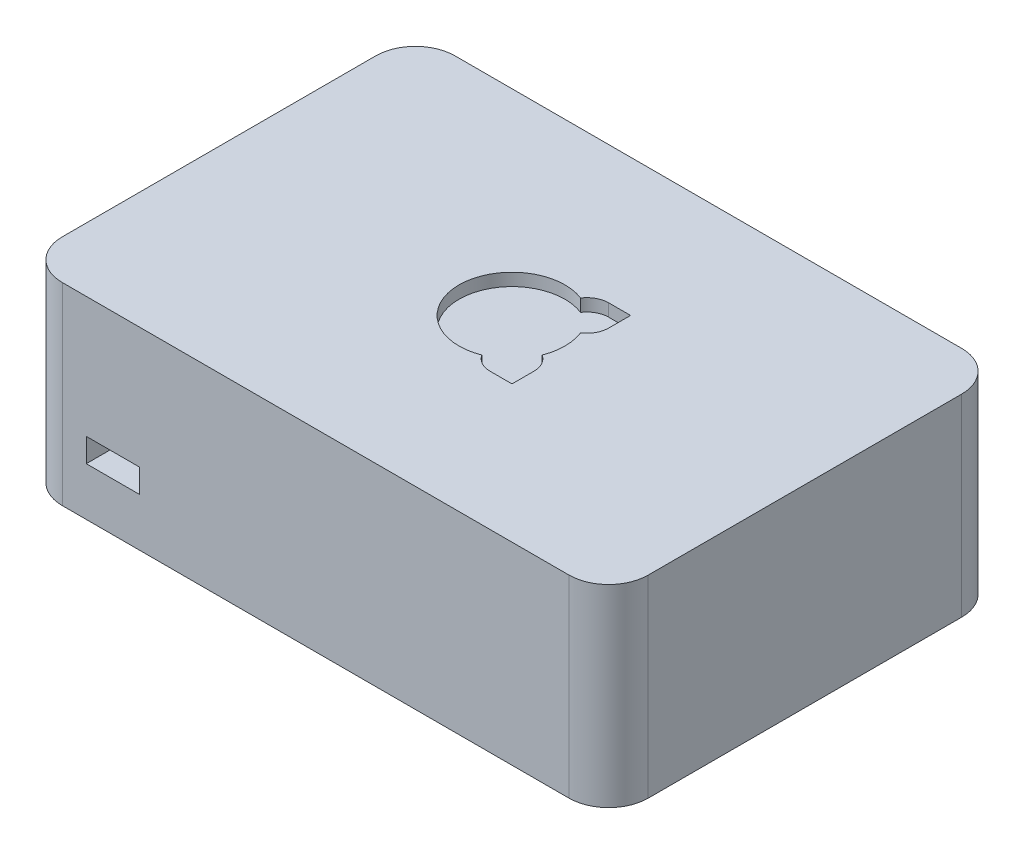
SolidWorks part; units mm, degrees
ref_plane "Front Plane" through (0, 0, 0) normal (0, 0, 1) x (1, 0, 0)
ref_plane "Top Plane" through (0, 0, 0) normal (0, 1, 0) x (1, 0, 0)
ref_plane "Right Plane" through (0, 0, 0) normal (1, 0, 0) x (0, 0, -1)
sketch "Sketch1" plane through (0, 0, 0) normal (0, 1, 0) x (1, 0, 0)
  line L1 (0, 0) -> (94, 0)
  line L2 (0, 0) -> (0, 63)
  line L3 (0, 63) -> (94, 63)
  line L4 (94, 0) -> (94, 63)
  dimension "D1" = 63
  dimension "D2" = 94
extrude "Boss-Extrude1" add sketch "Sketch1" along normal blind 31 contours L2 L3 L4 L1
fillet "Fillet1" radius 6.35 4 edges at (0, 15.5, -63) (94, 15.5, -63) (94, 15.5, 0) (0, 15.5, 0)
sketch "Sketch3" plane through (0, 0, -63) normal (0, 0, -1) x (-1, 0, 0)
  line L0 (-6.35, 31) -> (-87.65, 31) construction
  line L1 (-12, 26.46) -> (-62.5, 26.46)
  line L2 (-12, 26.46) -> (-12, 28.46)
  line L3 (-12, 28.46) -> (-62.5, 28.46)
  line L4 (-62.5, 26.46) -> (-62.5, 28.46)
  line L5 (0, 31) -> (0, 0) construction
  dimension "D1" = 50.5
  dimension "D2" = 2
  dimension "D3" = 2.54
  dimension "D4" = 12
extrude "Boss-Extrude2" add sketch "Sketch3" along normal blind 2.5
sketch "Sketch4" plane through (0, 0, 0) normal (0, 0, 1) x (1, 0, 0)
  line L0 (6.35, 0) -> (87.65, 0) construction
  line L1 (10.2, 7.75) -> (18.7, 7.75)
  line L2 (10.2, 7.75) -> (10.2, 11.55)
  line L3 (10.2, 11.55) -> (18.7, 11.55)
  line L4 (18.7, 7.75) -> (18.7, 11.55)
  line L5 (0, 0) -> (0, 31) construction
  point P4 (14.45, 11.55)
  dimension "D1" = 8.5
  dimension "D2" = 3.8
  dimension "D3" = 7.75
  dimension "D4" = 10.2
extrude "Cut-Extrude1" cut sketch "Sketch4" against normal blind 8
sketch "Sketch5" plane through (0, 31, 0) normal (0, 1, 0) x (1, 0, 0)
  line L0 (0, 6.35) -> (94, 56.65) construction
  line L1 (94, 6.35) -> (94, 56.65) construction
  line L3 (40.9896, 25.4896) -> (53.0104, 25.4896) construction
  line L4 (40.9896, 25.4896) -> (40.9896, 37.5104) construction
  line L5 (40.9896, 37.5104) -> (53.0104, 37.5104) construction
  line L6 (53.0104, 25.4896) -> (53.0104, 37.5104) construction
  line L7 (40.9896, 25.4896) -> (53.0104, 37.5104) construction
  line L8 (40.9896, 37.5104) -> (53.0104, 25.4896) construction
  line L9 (56.5104, 37.5104) -> (53.0104, 37.5104)
  line L10 (56.5104, 37.5104) -> (56.5104, 41.0104)
  line L11 (56.5104, 41.0104) -> (53.0104, 41.0104)
  line L12 (53.0104, 37.5104) -> (53.0104, 41.0104)
  line L13 (56.5104, 25.4896) -> (53.0104, 25.4896)
  line L14 (56.5104, 25.4896) -> (56.5104, 21.9896)
  line L15 (56.5104, 21.9896) -> (53.0104, 21.9896)
  line L16 (53.0104, 25.4896) -> (53.0104, 21.9896)
  arc A0 (94, 56.65) -> (87.65, 63) centre (87.65, 56.65) ccw construction
  circle A1 centre (47, 31.5) radius 8.5
  circle A2 centre (53.0104, 37.5104) radius 3.5
  circle A3 centre (53.0104, 25.4896) radius 3.5
  dimension "D1" = 17
  dimension "D2" = 7
extrude "Cut-Extrude2" cut sketch "Sketch5" against normal blind 2 contours A2 L10 L11 | A3 L15 L14 | A1
sketch "Sketch6" plane through (0, 0, 0) normal (0, -1, 0) x (1, 0, 0)
  line L0 (0, -31.5) -> (94, -31.5) construction
  line L1 (94, -6.35) -> (94, -56.65) construction
  line L2 (0, -6.35) -> (0, -56.65) construction
  line L3 (6.35, 0) -> (87.65, 0) construction
  line L4 (47, 0) -> (47, -31.5) construction
  circle A0 centre (27.2, -31.5) radius 1.5875
  circle A1 centre (79, -31.5) radius 1.5875
  point P4 (94, -31.5)
  point P7 (0, -31.5)
  dimension "D1" = 3.175
  dimension "D2" = 51.8
  dimension "D3" = 15
extrude "Cut-Extrude3" cut sketch "Sketch6" against normal blind 5
